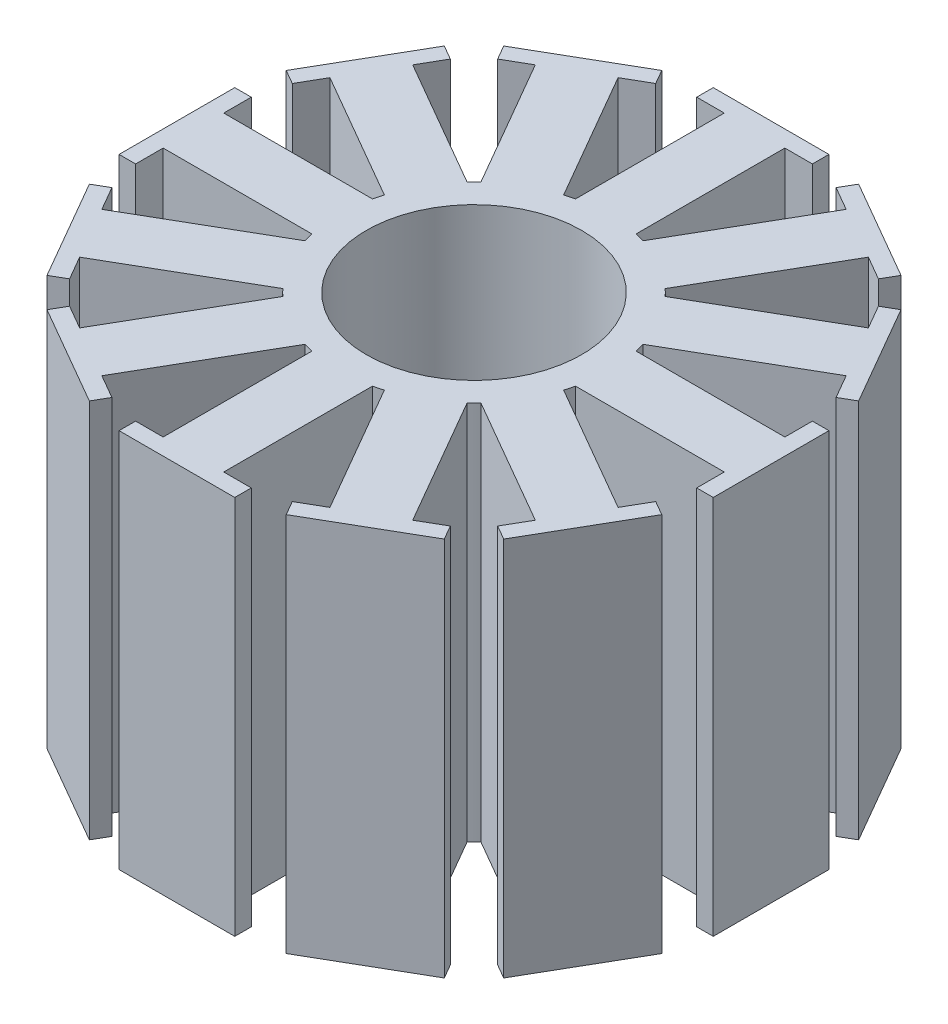
SolidWorks part; units mm, degrees
ref_plane "Front Plane" through (0, 0, 0) normal (0, 0, 1) x (1, 0, 0)
ref_plane "Top Plane" through (0, 0, 0) normal (0, 1, 0) x (1, 0, 0)
ref_plane "Right Plane" through (0, 0, 0) normal (1, 0, 0) x (0, 0, -1)
sketch "Sketch2" plane through (0, 0, 0) normal (0, 1, 0) x (1, 0, 0)
  circle A0 centre (0, 0) radius 3.91
  circle A1 centre (0, 0) radius 4.91
  dimension "D1" = 1
  dimension "D2" = 7.82
extrude "Boss-Extrude1" add sketch "Sketch2" along normal blind 13.8
sketch "Sketch3" plane through (0, 13.8, 0) normal (0, 1, 0) x (1, 0, 0)
  line L0 (4.7852, 1.1) -> (10.1852, 1.1)
  line L1 (10.1852, 1.1) -> (10.1852, 2.1)
  line L2 (10.1852, 2.1) -> (10.7852, 2.1)
  line L3 (10.7852, 2.1) -> (10.7852, -2.1)
  line L4 (10.7852, -2.1) -> (10.1852, -2.1)
  line L5 (10.1852, -2.1) -> (10.1852, -1.1)
  line L6 (10.1852, -1.1) -> (4.7852, -1.1)
  line L7 (0, 0) -> (-3.91, 0) construction
  line L8 (10.7852, 0) -> (7.0808, 0) construction
  line L9 (4.6941, -1.44) -> (9.3706, -4.14)
  line L10 (9.3706, -4.14) -> (9.8706, -3.2739)
  line L11 (9.8706, -3.2739) -> (10.3903, -3.5739)
  line L12 (10.3903, -3.5739) -> (8.2903, -7.2113)
  line L13 (8.2903, -7.2113) -> (7.7706, -6.9113)
  line L14 (7.7706, -6.9113) -> (8.2706, -6.0452)
  line L15 (8.2706, -6.0452) -> (3.5941, -3.3452)
  line L16 (3.3452, -3.5941) -> (6.0452, -8.2706)
  line L17 (6.0452, -8.2706) -> (6.9113, -7.7706)
  line L18 (6.9113, -7.7706) -> (7.2113, -8.2903)
  line L19 (7.2113, -8.2903) -> (3.5739, -10.3903)
  line L20 (3.5739, -10.3903) -> (3.2739, -9.8706)
  line L21 (3.2739, -9.8706) -> (4.14, -9.3706)
  line L22 (4.14, -9.3706) -> (1.44, -4.6941)
  line L23 (1.1, -4.7852) -> (1.1, -10.1852)
  line L24 (1.1, -10.1852) -> (2.1, -10.1852)
  line L25 (2.1, -10.1852) -> (2.1, -10.7852)
  line L26 (2.1, -10.7852) -> (-2.1, -10.7852)
  line L27 (-2.1, -10.7852) -> (-2.1, -10.1852)
  line L28 (-2.1, -10.1852) -> (-1.1, -10.1852)
  line L29 (-1.1, -10.1852) -> (-1.1, -4.7852)
  line L30 (-1.44, -4.6941) -> (-4.14, -9.3706)
  line L31 (-4.14, -9.3706) -> (-3.2739, -9.8706)
  line L32 (-3.2739, -9.8706) -> (-3.5739, -10.3903)
  line L33 (-3.5739, -10.3903) -> (-7.2113, -8.2903)
  line L34 (-7.2113, -8.2903) -> (-6.9113, -7.7706)
  line L35 (-6.9113, -7.7706) -> (-6.0452, -8.2706)
  line L36 (-6.0452, -8.2706) -> (-3.3452, -3.5941)
  line L37 (-3.5941, -3.3452) -> (-8.2706, -6.0452)
  line L38 (-8.2706, -6.0452) -> (-7.7706, -6.9113)
  line L39 (-7.7706, -6.9113) -> (-8.2903, -7.2113)
  line L40 (-8.2903, -7.2113) -> (-10.3903, -3.5739)
  line L41 (-10.3903, -3.5739) -> (-9.8706, -3.2739)
  line L42 (-9.8706, -3.2739) -> (-9.3706, -4.14)
  line L43 (-9.3706, -4.14) -> (-4.6941, -1.44)
  line L44 (-4.7852, -1.1) -> (-10.1852, -1.1)
  line L45 (-10.1852, -1.1) -> (-10.1852, -2.1)
  line L46 (-10.1852, -2.1) -> (-10.7852, -2.1)
  line L47 (-10.7852, -2.1) -> (-10.7852, 2.1)
  line L48 (-10.7852, 2.1) -> (-10.1852, 2.1)
  line L49 (-10.1852, 2.1) -> (-10.1852, 1.1)
  line L50 (-10.1852, 1.1) -> (-4.7852, 1.1)
  line L51 (-4.6941, 1.44) -> (-9.3706, 4.14)
  line L52 (-9.3706, 4.14) -> (-9.8706, 3.2739)
  line L53 (-9.8706, 3.2739) -> (-10.3903, 3.5739)
  line L54 (-10.3903, 3.5739) -> (-8.2903, 7.2113)
  line L55 (-8.2903, 7.2113) -> (-7.7706, 6.9113)
  line L56 (-7.7706, 6.9113) -> (-8.2706, 6.0452)
  line L57 (-8.2706, 6.0452) -> (-3.5941, 3.3452)
  line L58 (-3.3452, 3.5941) -> (-6.0452, 8.2706)
  line L59 (-6.0452, 8.2706) -> (-6.9113, 7.7706)
  line L60 (-6.9113, 7.7706) -> (-7.2113, 8.2903)
  line L61 (-7.2113, 8.2903) -> (-3.5739, 10.3903)
  line L62 (-3.5739, 10.3903) -> (-3.2739, 9.8706)
  line L63 (-3.2739, 9.8706) -> (-4.14, 9.3706)
  line L64 (-4.14, 9.3706) -> (-1.44, 4.6941)
  line L65 (-1.1, 4.7852) -> (-1.1, 10.1852)
  line L66 (-1.1, 10.1852) -> (-2.1, 10.1852)
  line L67 (-2.1, 10.1852) -> (-2.1, 10.7852)
  line L68 (-2.1, 10.7852) -> (2.1, 10.7852)
  line L69 (2.1, 10.7852) -> (2.1, 10.1852)
  line L70 (2.1, 10.1852) -> (1.1, 10.1852)
  line L71 (1.1, 10.1852) -> (1.1, 4.7852)
  line L72 (1.44, 4.6941) -> (4.14, 9.3706)
  line L73 (4.14, 9.3706) -> (3.2739, 9.8706)
  line L74 (3.2739, 9.8706) -> (3.5739, 10.3903)
  line L75 (3.5739, 10.3903) -> (7.2113, 8.2903)
  line L76 (7.2113, 8.2903) -> (6.9113, 7.7706)
  line L77 (6.9113, 7.7706) -> (6.0452, 8.2706)
  line L78 (6.0452, 8.2706) -> (3.3452, 3.5941)
  line L79 (3.5941, 3.3452) -> (8.2706, 6.0452)
  line L80 (8.2706, 6.0452) -> (7.7706, 6.9113)
  line L81 (7.7706, 6.9113) -> (8.2903, 7.2113)
  line L82 (8.2903, 7.2113) -> (10.3903, 3.5739)
  line L83 (10.3903, 3.5739) -> (9.8706, 3.2739)
  line L84 (9.8706, 3.2739) -> (9.3706, 4.14)
  line L85 (9.3706, 4.14) -> (4.6941, 1.44)
  circle A0 centre (0, 0) radius 4.91 construction
  arc A1 (4.7852, -1.1) -> (4.7852, 1.1) centre (0, 0) ccw
  circle A2 centre (0, 0) radius 3.91 construction
  arc A3 (3.5941, -3.3452) -> (4.6941, -1.44) centre (0, 0) ccw
  arc A4 (1.44, -4.6941) -> (3.3452, -3.5941) centre (0, 0) ccw
  arc A5 (-1.1, -4.7852) -> (1.1, -4.7852) centre (0, 0) ccw
  arc A6 (-3.3452, -3.5941) -> (-1.44, -4.6941) centre (0, 0) ccw
  arc A7 (-4.6941, -1.44) -> (-3.5941, -3.3452) centre (0, 0) ccw
  arc A8 (-4.7852, 1.1) -> (-4.7852, -1.1) centre (0, 0) ccw
  arc A9 (-3.5941, 3.3452) -> (-4.6941, 1.44) centre (0, 0) ccw
  arc A10 (-1.44, 4.6941) -> (-3.3452, 3.5941) centre (0, 0) ccw
  arc A11 (1.1, 4.7852) -> (-1.1, 4.7852) centre (0, 0) ccw
  arc A12 (3.3452, 3.5941) -> (1.44, 4.6941) centre (0, 0) ccw
  arc A13 (4.6941, 1.44) -> (3.5941, 3.3452) centre (0, 0) ccw
  point P107 (0, 0)
  dimension "D1" = 0.6
  dimension "D2" = 2.2
  dimension "D3" = 6
  dimension "D4" = 1
  dimension "D5" = 12
extrude "Boss-Extrude2" add sketch "Sketch3" along direction (0, 1, 0) on the side against the normal blind 13.8
